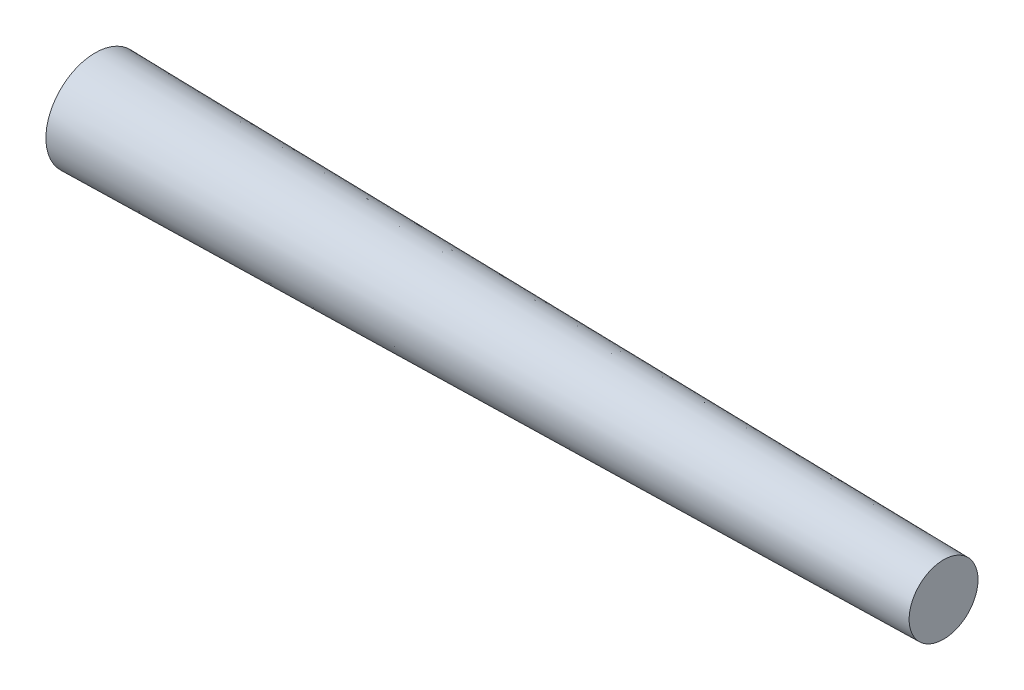
SolidWorks part; units mm, degrees
ref_plane "Front Plane" through (0, 0, 0) normal (0, 0, 1) x (1, 0, 0)
ref_plane "Top Plane" through (0, 0, 0) normal (0, 1, 0) x (1, 0, 0)
ref_plane "Right Plane" through (0, 0, 0) normal (1, 0, 0) x (0, 0, -1)
sketch "Sketch1" plane through (0, 0, 0) normal (1, 0, 0) x (0, 0, -1)
  circle A0 centre (0, 0) radius 5.05
  dimension "D1" = 10.1
extrude "Boss-Extrude1" add sketch "Sketch1" along normal blind 87 draft 1
sketch "Sketch2" plane through (0, 0, 0) normal (0, 1, 0) x (1, 0, 0)
  line L0 (0, 1) -> (-1, 1)
  line L1 (0, 5.05) -> (0, -5.05) construction
  line L2 (-1, -1) -> (0, -1)
  line L3 (0, 1) -> (0, -1)
  arc A0 (-1, 1) -> (-1, -1) centre (-1, 0) ccw
  circle A1 centre (-1, 0) radius 0.5
  dimension "D1" = 1
  dimension "D3" = 1
  dimension "D2" = 1
extrude "Boss-Extrude2" add sketch "Sketch2" along normal mid plane 1
